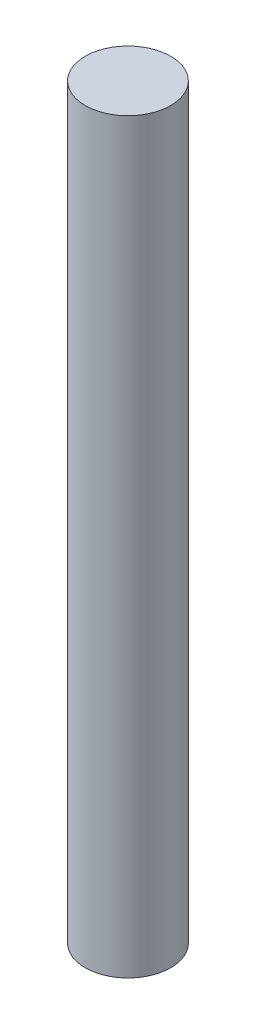
SolidWorks part; units mm, degrees
ref_plane "Front Plane" through (0, 0, 0) normal (0, 0, 1) x (1, 0, 0)
ref_plane "Top Plane" through (0, 0, 0) normal (0, 1, 0) x (1, 0, 0)
ref_plane "Right Plane" through (0, 0, 0) normal (1, 0, 0) x (0, 0, -1)
sketch "Sketch1" plane through (0, 0, 0) normal (0, 1, 0) x (1, 0, 0)
  circle A0 centre (0, 0) radius 2.5
  dimension "D1" = 5
extrude "Boss-Extrude1" add sketch "Sketch1" along normal blind 43.7
